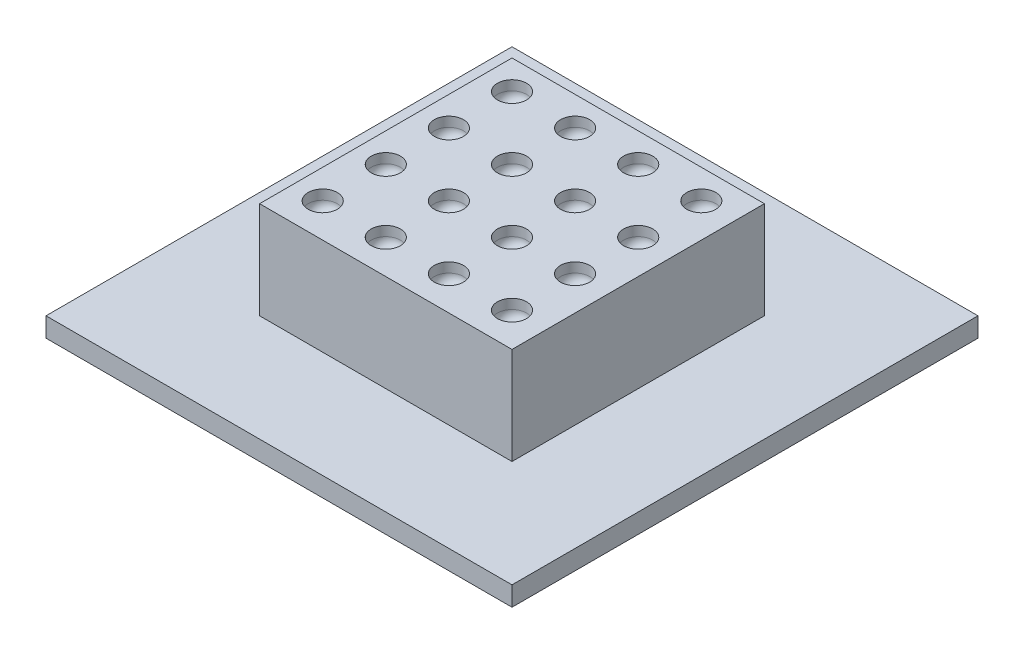
SolidWorks part; units mm, degrees
ref_plane "Front Plane" through (0, 0, 0) normal (0, 0, 1) x (1, 0, 0)
ref_plane "Top Plane" through (0, 0, 0) normal (0, 1, 0) x (1, 0, 0)
ref_plane "Right Plane" through (0, 0, 0) normal (1, 0, 0) x (0, 0, -1)
sketch "Sketch1" plane through (0, 0, 0) normal (0, 1, 0) x (1, 0, 0)
  line L1 (6.5, -6.5) -> (-6.5, -6.5)
  line L2 (6.5, -6.5) -> (6.5, 6.5)
  line L3 (6.5, 6.5) -> (-6.5, 6.5)
  line L4 (-6.5, -6.5) -> (-6.5, 6.5)
  line L5 (6.5, -6.5) -> (-6.5, 6.5) construction
  line L6 (6.5, 6.5) -> (-6.5, -6.5) construction
  point P0 (0, 0)
  dimension "D1" = 13
extrude "Boss-Extrude1" add sketch "Sketch1" along normal blind 5
sketch "Sketch2" plane through (0, 0, 0) normal (0, -1, 0) x (1, 0, 0)
  line L8 (-12, 12) -> (-12, -12)
  line L9 (-12, -12) -> (12, -12)
  line L10 (12, -12) -> (12, 12)
  line L11 (12, 12) -> (-12, 12)
  line L12 (-12, 12) -> (-12, -12)
  line L13 (-12, -12) -> (12, -12)
  line L14 (12, -12) -> (12, 12)
  line L15 (12, 12) -> (-12, 12)
  dimension "D1" = 5.5
extrude "Boss-Extrude2" add sketch "Sketch2" along normal blind 1
sketch "Sketch3" plane through (0, 5, 0) normal (0, 1, 0) x (1, 0, 0)
  line L0 (6.5, 6.5) -> (-6.5, 6.5) construction
  line L1 (-6.5, 6.5) -> (-6.5, -6.5) construction
  circle A0 centre (-5, 5) radius 0.75
  dimension "D1" = 1.5
  dimension "D2" = 1.5
  dimension "D3" = 1.5
extrude "Cut-Extrude1" cut sketch "Sketch3" against normal blind 1
fillet "Fillet1" radius 0.5 1 edges at (-5, 4, -4.25)
pattern_linear "LPattern1" count 4 spacing 3.25 along (1, 0, 0) count 4 spacing 3.25 along (0, 0, 1) of "Cut-Extrude1", "Fillet1"
